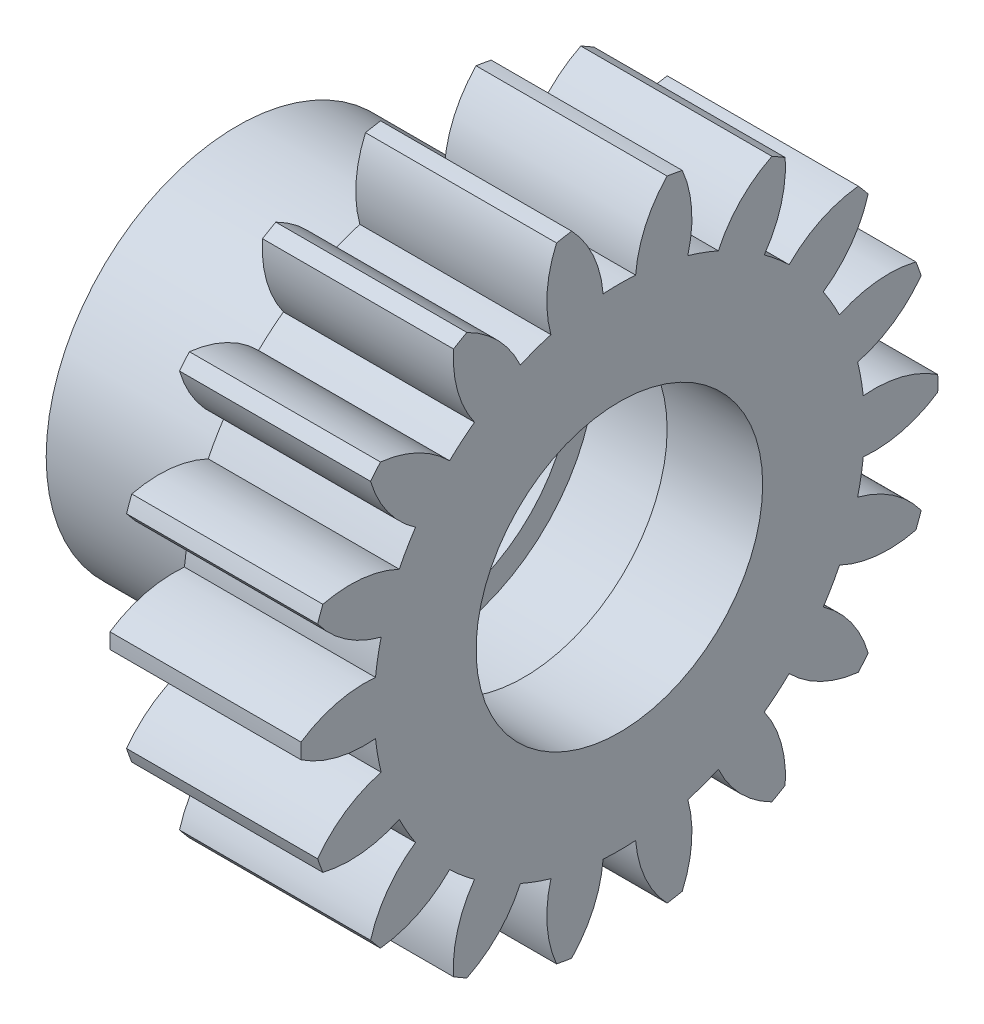
SolidWorks part; units mm, degrees
material "PET"
ref_plane "Plane1" through (0, 0, 0) normal (0, 0, 1) x (1, 0, 0)
ref_plane "Plane2" through (0, 0, 0) normal (0, 1, 0) x (1, 0, 0)
ref_plane "Plane3" through (0, 0, 0) normal (1, 0, 0) x (0, 0, -1)
sketch "HoldingSke" plane through (0, 0, 0) normal (0, 1, 0) x (1, 0, 0)
  line L0 (0, 0) -> (1159.5281, -376.7535)
  line L1 (-15, 0) -> (100, 0) construction
  line L2 (0, 0) -> (-2.1039, 2.3779)
  line L3 (0, 0) -> (-11.863, 4.5341)
  line L4 (0, 0) -> (8.2133, 2.6687)
  line L5 (0, 0) -> (-47.5972, -17.7524)
  line L6 (0, 0) -> (-2.632, -1.7758)
  line L7 (-2.1039, 2.3779) -> (8.831, 51.988)
  line L8 (-76.2, 54.61) -> (-75.184, 54.61)
  line L9 (-71.009, 38.7566) -> (-53.1078, 45.2721)
  line L10 (-76.2, 71.12) -> (104.1128, 71.12)
  line L11 (0, 0) -> (-3.175, 0)
  line L12 (-76.2, 101.6) -> (-76.1787, 101.6)
  line L13 (24.9733, 27.94) -> (52.9518, 28.4284)
  line L14 (24.9733, 27.94) -> (25.0241, 27.9398)
  line L15 (24.9733, 27.94) -> (100.4021, 29.52)
  circle A0 centre (0, 0) radius 0.3969
  circle A1 centre (0, 0) radius 4.0767
  circle A2 centre (0, 0) radius 38.1
  circle A3 centre (0, 0) radius 0.3969
  dimension "MHD" = 8.1534
  dimension "Hub_dia" = 76.2
  dimension "Bore" = 0.7937
  dimension "MBD" = 0.7937
  dimension "Num_teeth" = 18
  dimension "Pitch" = 1219.2
  dimension "Overall_len" = 50.8
  dimension "Show_teeth" = 18
  dimension "Thickness" = 3.175
  dimension "OAL" = 50.8009
  dimension "T_dim" = 1.016
  dimension "Ap" = 20
  dimension "H" = 19.05
  dimension "Pitch_radius" = 180.3128
  dimension "Width" = 3.175
  dimension "Backlash" = 0.0213
  dimension "Addendum_fac" = 1
  dimension "Dedendum_fac" = 1.2
  dimension "Clearance_fac" = 0.2
  dimension "Dedendum_add" = 0.0508
sketch "BasProSke" plane through (0, 0, 0) normal (0, 1, 0) x (1, 0, 0)
  line L0 (-10, 0) -> (60, 0) construction
  line L1 (0, 0) -> (0, 5.2917)
  line L2 (0, 0) -> (3.175, 0)
  line L3 (3.175, 0) -> (3.175, 5.2917)
  line L4 (3.175, 5.2917) -> (0, 5.2917)
  dimension "Thickness" = 3.175
  dimension "Diameter" = 10.5833
revolve "Base-Revolve" add sketch "BasProSke" angle 360 about L0
sketch "TooCutSke" plane through (0, 0, 0) normal (1, 0, 0) x (0, 0, -1)
  line L1 (0, 0) -> (0, 107) construction
  line L2 (0, 0) -> (-0.4524, 4.741) construction
  line L3 (0, 0) -> (-1.6488, 9.3507) construction
  line L4 (-0.4524, 4.741) -> (-0.8244, 4.6754) construction
  arc A0 (0.27, 4.0677) -> (-0.27, 4.0677) centre (0, 0) ccw
  arc A1 (0.8145, 5.2543) -> (-0.8145, 5.2543) centre (0, 0) ccw
  circle A2 centre (0, 0) radius 4.7625 construction
  circle A3 centre (0, 0) radius 4.4753 construction
  arc A4 (-0.27, 4.0677) -> (-0.8145, 5.2543) centre (-2.1688, 3.9146) ccw
  arc A5 (0.8145, 5.2543) -> (0.27, 4.0677) centre (2.1688, 3.9146) ccw
  dimension "Root_dia" = 8.1534
  dimension "Overcut_dia" = 10.6341
  dimension "Pitch_dia" = 9.525
  dimension "Base_dia" = 8.9506
  dimension "Flank_rad" = 1.905
  dimension "Half_ang" = 10
  dimension "Half_CT" = 0.3777
extrude "ToothCut" cut sketch "TooCutSke" along normal through all
fillet "Breaks" [suppressed] radius 0.0106
fillet "RootFillets" [suppressed] radius 0.1566
pattern_circular "TeethCuts" count 18 every 20 about axis through (-10, 0, 0) along (1, 0, 0) of "ToothCut", "RootFillets", "Breaks"
sketch "HubNeaOneSke" plane through (0, 0, 0) normal (-1, 0, 0) x (0, 0, 1)
  circle A0 centre (0, 0) radius 4.0767
  dimension "Diameter" = 8.1534
extrude "HubNearOne" [suppressed] add sketch "HubNeaOneSke" along normal blind 47.6259
sketch "HubNeaBotSke" plane through (0, 0, 0) normal (-1, 0, 0) x (0, 0, 1)
  circle A0 centre (0, 0) radius 4.0767
  dimension "Diameter" = 8.1534
extrude "HubNearBoth" [suppressed] add sketch "HubNeaBotSke" along normal blind 23.813
ref_plane "FarPln" through (3.175, 0, 0) normal (1, 0, 0) x (0, 0, -1)
sketch "HubFarSke" plane through (3.175, 0, 0) normal (1, 0, 0) x (0, 0, -1)
  circle A0 centre (0, 0) radius 4.0767
  dimension "Diameter" = 8.1534
extrude "HubFar" [suppressed] add sketch "HubFarSke" along normal blind 23.813
sketch "BorSke" plane through (0, 0, 0) normal (1, 0, 0) x (0, 0, -1)
  circle A0 centre (0, 0) radius 0.3969
  dimension "Diameter" = 0.7937
extrude "Bore" cut sketch "BorSke" along normal mid plane 101.6018
sketch "KeySke" plane through (0, 0, 0) normal (1, 0, 0) x (0, 0, -1)
  line L0 (-0.127, 0) -> (-0.127, 0.6191)
  line L1 (-0.127, 0.6191) -> (0.127, 0.6191)
  line L2 (0.127, 0.6191) -> (0.127, 0)
  line L3 (0, 0) -> (0, 34) construction
  line L4 (-0.127, 0) -> (0.127, 0)
  dimension "Offset" = 0.6191
  dimension "Width" = 0.254
extrude "Keyway" [suppressed] cut sketch "KeySke" along normal mid plane 101.6018
pattern_circular "Keyway2" [suppressed] count 2 every 90 about axis through (-10, 0, 0) along (1, 0, 0)
sketch "Sketch1" plane through (0, 0, 0) normal (-1, 0, 0) x (0, 0, 1)
  circle A0 centre (0, 0) radius 2.7781
  dimension "D1" = 5.5562
extrude "Cut-Extrude2" cut sketch "Sketch1" against normal offset from surface (1.5875 mm away) 1.5875 up to face at (3.175, 0, 0.3969)
ref_plane "Plane4" through (1.5875, 0, 0) normal (1, 0, 0) x (0, 0, -1)
sketch "Sketch2" plane through (1.5875, 0, 0) normal (1, 0, 0) x (0, 0, -1)
  circle A0 centre (0, 0) radius 4.7625
  dimension "D1" = 9.525
sketch "Sketch3" plane through (0, 0, 0) normal (-1, 0, 0) x (0, 0, 1)
  circle A0 centre (0, 0) radius 3.175
  circle A1 centre (0, 0) radius 0.3969 construction
  circle A2 centre (0, 0) radius 0.3969
  dimension "D1" = 6.35
extrude "Boss-Extrude1" add sketch "Sketch3" along normal blind 3.175
sketch "Sketch4" plane through (3.175, 0, 0) normal (1, 0, 0) x (0, 0, -1)
  circle A0 centre (0, 0) radius 2.3813
  dimension "D1" = 4.7625
extrude "Cut-Extrude3" cut sketch "Sketch4" against normal offset from surface (4.7625 mm away) 1.5875 up to face at (-3.175, 0, 3.175)
equation "' \"Pitch@HoldingSke\" = 4"
equation "'\"Num_teeth@HoldingSke\" = 18"
equation "'\"Ap@HoldingSke\" =  20"
equation "'\"Ap@HoldingSke\" = 20"
equation "' \"Width@HoldingSke\" = 0.5"
equation "' \"Hub_dia@HoldingSke\"= 1"
equation "' \"Hub_dia@HoldingSke\" = 1"
equation "' \"Overall_len@HoldingSke\" = 1.0"
equation "' \"Bore@HoldingSke\" = 0.75"
equation "' \"T_dim@HoldingSke\" = 0.85"
equation "' \"Width@KeySke\" = 0.25"
equation "' \"Show_teeth@HoldingSke\" = 13"
equation "' \"Backlash@HoldingSke\" = 0.009"
equation "' \"Addendum_fac@HoldingSke\" = 1.0"
equation "' \"Dedendum_fac@HoldingSke\" = 1.25"
equation "' \"Dedendum_add@HoldingSke\" = 0.00005"
equation "' \"Clearance_fac@HoldingSke\" = 0.25"
equation "' \"Pitch@HoldingSke\" = 0.5"
equation "' \"Num_teeth@HoldingSke\" = 23"
equation "' \"Ap@HoldingSke\" =  20"
equation "' \"Ap@HoldingSke\" = 20"
equation "' \"Show_teeth@HoldingSke\" = 23"
equation "' \"Backlash@HoldingSke\" = 0.0375"
equation "\"Overcut_dia@TooCutSke\" = (\"Num_teeth@HoldingSke\" + 2 * \"Addendum_fac@HoldingSke\") / \"Pitch@HoldingSke\" + 0.002"
equation "\"Pitch_dia@TooCutSke\" = \"Num_teeth@HoldingSke\" / \"Pitch@HoldingSke\""
equation "\"Base_dia@TooCutSke\" = \"Num_teeth@HoldingSke\" / \"Pitch@HoldingSke\" * cos((\"Ap@HoldingSke\"  * 3.14159265 / 180))"
equation "\"Root_dia@TooCutSke\" = (\"Num_teeth@HoldingSke\" + 2) / \"Pitch@HoldingSke\" - 2 * (\"Addendum_fac@HoldingSke\" + \"Dedendum_fac@HoldingSke\") / \"Pitch@HoldingSke\" - \"Dedendum_add@HoldingSke\" * 2"
equation "\"Half_ang@TooCutSke\" = 180 / \"Num_teeth@HoldingSke\""
equation "\"Half_CT@TooCutSke\" = \"Num_teeth@HoldingSke\" / \"Pitch@HoldingSke\" * sin((3.14159265 / 2 / \"Num_teeth@HoldingSke\")) / 2 - 7 * \"Backlash@HoldingSke\" / 4"
equation "\"Flank_rad@TooCutSke\" = \"Num_teeth@HoldingSke\" / \"Pitch@HoldingSke\" / 5"
equation "\"Radius@RootFillets\" = \"Clearance_fac@HoldingSke\" / \"Pitch@HoldingSke\" + \"Dedendum_add@HoldingSke\""
equation "\"Break_rad@Breaks\" = 0.02 / \"Pitch@HoldingSke\""
equation "\"Thickness@HoldingSke\" = \"Width@HoldingSke\""
equation "\"OAL@HoldingSke\" = \"Thickness@HoldingSke\""
equation "\"MHD@HoldingSke\" = (\"Num_teeth@HoldingSke\" + 2) / \"Pitch@HoldingSke\" - 2 * (\"Addendum_fac@HoldingSke\" + \"Dedendum_fac@HoldingSke\")  / \"Pitch@HoldingSke\" - \"Dedendum_add@HoldingSke\" * 2"
equation "\"MBD@HoldingSke\" = (\"Num_teeth@HoldingSke\" + 2) / \"Pitch@HoldingSke\" - 2 * (\"Addendum_fac@HoldingSke\" + \"Dedendum_fac@HoldingSke\")  / \"Pitch@HoldingSke\" - \"Dedendum_add@HoldingSke\" * 2 - 0.002"
equation "\"MHD@HoldingSke\" = ((sgn( \"MHD@HoldingSke\" - \"Hub_dia@HoldingSke\" )-1)*( \"MHD@HoldingSke\" - \"Hub_dia@HoldingSke\" ))/-2+ \"Hub_dia@HoldingSke\""
equation "\"MBD@HoldingSke\" = ((sgn( \"MBD@HoldingSke\" - \"Bore@HoldingSke\" )-1)*( \"MBD@HoldingSke\" - \"Bore@HoldingSke\" ))/-2+ \"Bore@HoldingSke\""
equation "\"OAL@HoldingSke\" = ((sgn( \"OAL@HoldingSke\" - \"Overall_len@HoldingSke\" )+1)*( \"OAL@HoldingSke\" - \"Overall_len@HoldingSke\" ))/2 + \"Overall_len@HoldingSke\" + 0.000002"
equation "\"Num_teeth@TeethCuts\" = int( \"Show_teeth@HoldingSke\" ) + 1"
equation "\"Num_teeth@TeethCuts\" = ((sgn( \"Num_teeth@TeethCuts\" - \"Num_teeth@HoldingSke\" )-1)*( \"Num_teeth@TeethCuts\" - \"Num_teeth@HoldingSke\" ))/-2+ \"Num_teeth@HoldingSke\""
equation "\"Num_teeth@TeethCuts\" = ((sgn( \"Num_teeth@TeethCuts\" - 2.0)+1)*( \"Num_teeth@TeethCuts\" - 2.0))/2 +2.0"
equation "\"Angle@TeethCuts\" = 360.0 / \"Num_teeth@HoldingSke\""
equation "\"Diameter@BasProSke\" = (\"Num_teeth@HoldingSke\" + 2 * \"Addendum_fac@HoldingSke\") / \"Pitch@HoldingSke\""
equation "\"Thickness@BasProSke\"  = \"Thickness@HoldingSke\""
equation "' \"Fillet_rad@BasProSke\" =  \"Thickness@HoldingSke\" * 0.05"
equation "' \"Fillet_rad@BasProSke\" = \"Thickness@HoldingSke\" * 0.05"
equation "\"MHD@HoldingSke\" = ((sgn( \"MHD@HoldingSke\" - \"Root_dia@TooCutSke\" )-1)*( \"MHD@HoldingSke\" - \"Root_dia@TooCutSke\" ))/-2+ \"Root_dia@TooCutSke\""
equation "\"Diameter@HubNeaOneSke\" = \"MHD@HoldingSke\""
equation "\"Length@HubNearOne\" = \"OAL@HoldingSke\" - \"Thickness@BasProSke\""
equation "\"Diameter@HubNeaBotSke\" = \"MHD@HoldingSke\""
equation "\"Length@HubNearBoth\" = ( \"OAL@HoldingSke\" - \"Thickness@BasProSke\" ) / 2.0"
equation "\"Thickness@FarPln\" = \"Thickness@BasProSke\""
equation "\"Diameter@HubFarSke\" = \"MHD@HoldingSke\""
equation "\"Length@HubFar\" = ( \"OAL@HoldingSke\" - \"Thickness@BasProSke\" ) / 2.0"
equation "\"Diameter@BorSke\" = \"MBD@HoldingSke\""
equation "\"D1@Bore\" = \"OAL@HoldingSke\" * 2.0"
equation "\"D1@Keyway\" = \"OAL@HoldingSke\" * 2.0"
equation "\"Offset@KeySke\" = \"T_dim@HoldingSke\" - \"MBD@HoldingSke\" / 2.0"
